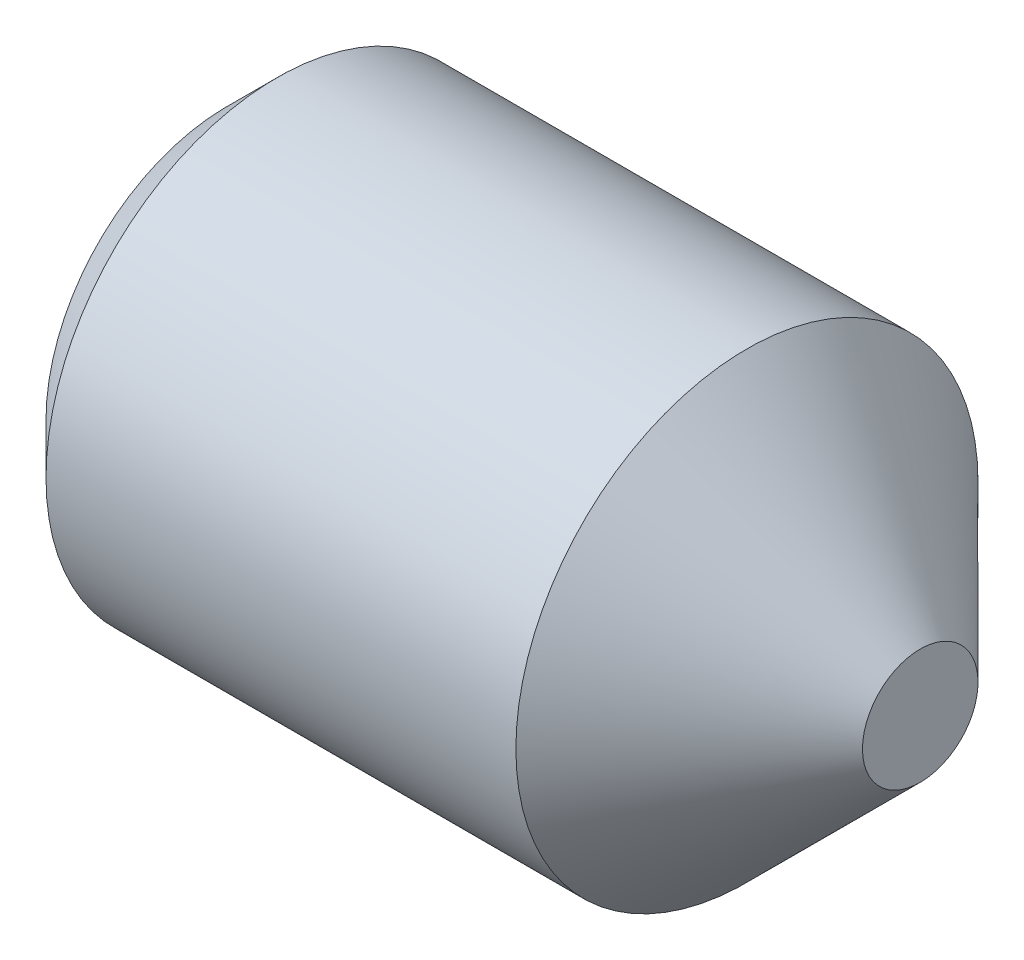
SolidWorks part; units mm, degrees
ref_plane "Front" through (0, 0, 0) normal (0, 0, 1) x (1, 0, 0)
ref_plane "Top" through (0, 0, 0) normal (0, 1, 0) x (1, 0, 0)
ref_plane "Right" through (0, 0, 0) normal (1, 0, 0) x (0, 0, -1)
sketch "Sketch1" plane through (0, 0, 0) normal (0, 0, 1) x (1, 0, 0)
  line L0 (0, 0) -> (3, 0)
  line L1 (3, 0) -> (3, 0.25)
  line L2 (3, 0.25) -> (2.25, 1)
  line L3 (2.25, 1) -> (0.2165, 1)
  line L4 (0.2165, 1) -> (0, 0.7835)
  line L5 (0, 0.7835) -> (0, 0)
  line L6 (-14.7741, 0) -> (12.5137, 0) construction
  dimension "l" = 3
  dimension "df" = 2.459
  dimension "D1" = 45
  dimension "D2" = 45
revolve "Base" add sketch "Sketch1" angle 360 about L6
cosmetic thread "ThreadCosmetic1" [suppressed] parameters "D2"=1.567
sketch "Sketch2" plane through (0, 0.2203, -0.1392) normal (-1, 0, 0) x (0, 0, 1)
  line L1 (0.6588, -0.2203) -> (0.399, 0.2297)
  line L2 (0.399, 0.2297) -> (-0.1206, 0.2297)
  line L3 (-0.1206, 0.2297) -> (-0.3804, -0.2203)
  line L4 (-0.3804, -0.2203) -> (-0.1206, -0.6703)
  line L5 (-0.1206, -0.6703) -> (0.399, -0.6703)
  line L6 (0.399, -0.6703) -> (0.6588, -0.2203)
  circle A0 centre (0.1392, -0.2203) radius 0.45 construction
  dimension "s" = 0.9
extrude "HexagonSocket" cut sketch "Sketch2" against normal blind 0.8
sketch "Sketch3" plane through (0, 0, 0) normal (0, 0, 1) x (1, 0, 0)
  line L0 (0.8, 0) -> (-2.4777, 0) construction
  line L2 (0.8, 0.45) -> (1.0598, 0)
  line L3 (1.0598, 0) -> (0.8, -0.45) construction
  line L4 (0.8, 0.45) -> (0.8, 0)
  line L5 (0.8, 0) -> (1.0598, 0)
  dimension "D1" = 120
revolve "Cut-Revolve" cut sketch "Sketch3" angle 360 about L0
sketch "Sketch4" plane through (0, 0, 0) normal (0, 0, 1) x (1, 0, 0)
  line L0 (0.2165, 0.8125) -> (0.3248, 1)
  line L1 (0.3248, 1) -> (0.3248, 1.2165)
  line L2 (0.3248, 1.2165) -> (0.1083, 1.2165)
  line L3 (0.1083, 1.2165) -> (0.1083, 1)
  line L4 (0.1083, 1) -> (0.2165, 0.8125)
  line L5 (0, 0) -> (3.2295, 0) construction
  line L6 (0.2165, 1) -> (0.2165, -1) construction
  dimension "D1" = 3
  dimension "D2" = 0.2705
revolve "Cut-Revolve10" [suppressed] cut sketch "Sketch4" angle 360 about L5
pattern_linear "LPattern10" [suppressed] count 9 spacing 0.3246 along (1, 0, 0)
equation "\"df@Sketch1\" = \"D2@ThreadCosmetic1\""
equation "\"D1@Sketch4\" = \"d@Sketch1\""
equation "\"D2@Sketch4\" =  ( \"d@Sketch1\" - \"D2@ThreadCosmetic1\" )  / 2"
equation "\"D3@LPattern10\" = \"D2@Sketch4\" * 1.2"
equation "\"D1@LPattern10\" = \"l@Sketch1\" / \"D3@LPattern10\""
